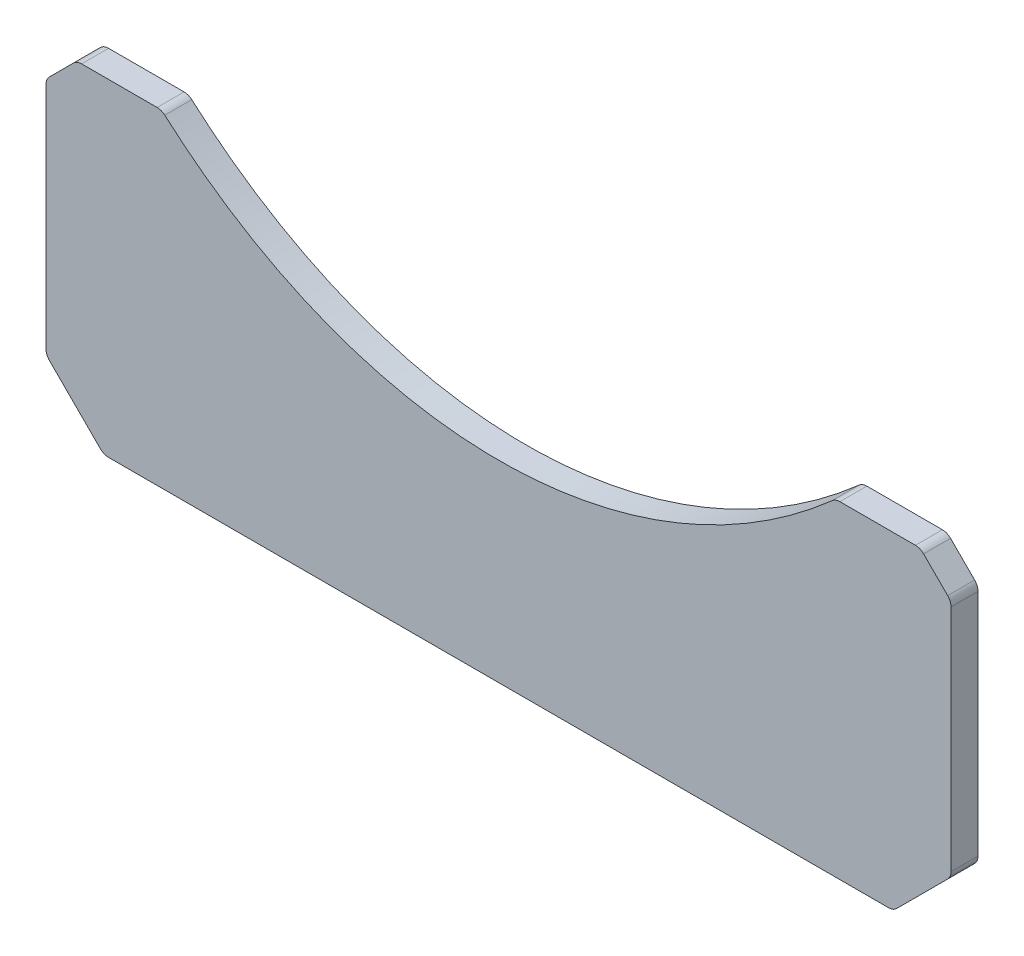
SolidWorks part; units mm, degrees
ref_plane "Plane1" through (0, 0, 0) normal (0, 0, 1) x (1, 0, 0)
ref_plane "Plane2" through (0, 0, 0) normal (0, 1, 0) x (1, 0, 0)
ref_plane "Plane3" through (0, 0, 0) normal (1, 0, 0) x (0, 0, -1)
sketch "Sketch1" plane through (0, 0, 0) normal (0, 0, 1) x (1, 0, 0)
  line L0 (-102.5, 0) -> (102.5, 0)
  line L1 (102.5, 0) -> (117.5, 15)
  line L2 (117.5, 15) -> (117.5, 77)
  line L3 (109.5, 85) -> (87.5, 85)
  line L4 (-117.5, 77) -> (-109.5, 85)
  line L5 (0, 0) -> (0, 230) construction
  line L6 (-102.5, 0) -> (-117.5, 15)
  line L7 (-117.5, 15) -> (-117.5, 77)
  line L8 (-109.5, 85) -> (-87.5, 85)
  line L9 (117.5, 77) -> (109.5, 85)
  ellipse E0 centre (0, 230) end of major axis (0, 410) minor radius 147.6743 (87.5, 85) -> (-87.5, 85) cw
  point P4 (117.5, 85)
  point P10 (-117.5, 85)
  dimension "D1" = 235
  dimension "D2" = 85
  dimension "D3" = 230
  dimension "D4" = 30
  dimension "D5" = 50
  dimension "D6" = 15
  dimension "D7" = 15
extrude "Base-Extrude" add sketch "Sketch1" along normal blind 7
fillet "Fillet1" radius 3 12 edges at (0, 50, 0) (0, 50, 7) (102.5, 0, 3.5) (-102.5, 0, 3.5) (-117.5, 15, 3.5) (-117.5, 77, 3.5) (-109.5, 85, 3.5) (-87.5, 85, 3.5) (87.5, 85, 3.5) (109.5, 85, 3.5) (117.5, 77, 3.5) (117.5, 15, 3.5)
